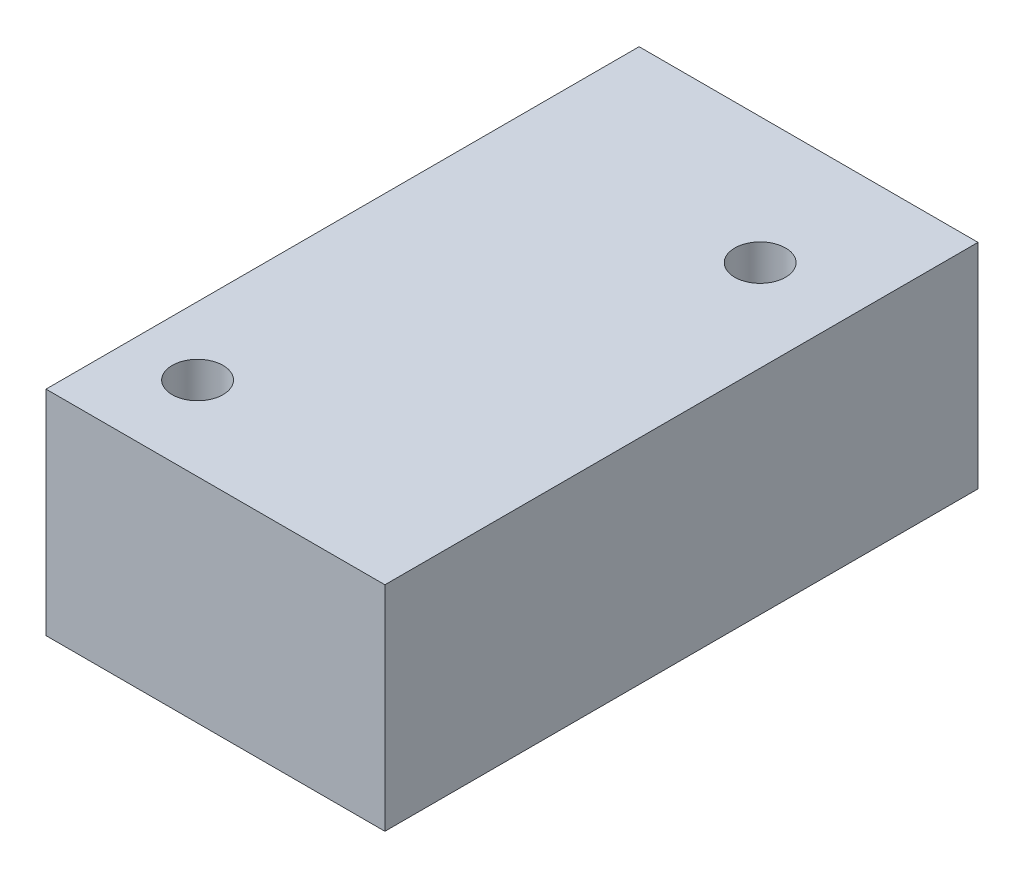
SolidWorks part; units mm, degrees
ref_plane "Front Plane" through (0, 0, 0) normal (0, 0, 1) x (1, 0, 0)
ref_plane "Top Plane" through (0, 0, 0) normal (0, 1, 0) x (1, 0, 0)
ref_plane "Right Plane" through (0, 0, 0) normal (1, 0, 0) x (0, 0, -1)
sketch "Sketch1" plane through (0, 0, 0) normal (0, 1, 0) x (1, 0, 0)
  line L1 (-10, 17.5) -> (10, 17.5)
  line L2 (-10, 17.5) -> (-10, -17.5)
  line L3 (-10, -17.5) -> (10, -17.5)
  line L4 (10, 17.5) -> (10, -17.5)
  line L5 (-10, 17.5) -> (10, -17.5) construction
  line L6 (-10, -17.5) -> (10, 17.5) construction
  point P0 (0, 0)
  dimension "D1" = 20
  dimension "D2" = 35
extrude "Boss-Extrude1" add sketch "Sketch1" along normal blind 12.6
sketch "Sketch2" plane through (0, 0, 0) normal (0, -1, 0) x (1, 0, 0)
  circle A0 centre (-5.9906, 12.5634) radius 1.5 construction
  circle A1 centre (4.6094, -10.0366) radius 1.5 construction
  circle A2 centre (-5.9906, 12.5634) radius 1.5
  circle A3 centre (4.6094, -10.0366) radius 1.5
extrude "Cut-Extrude1" cut sketch "Sketch2" against normal up to next
sketch "Sketch3" plane through (0, 0, 0) normal (0, 1, 0) x (1, 0, 0)
  line L4 (10, -17.5) -> (10, 17.5)
  line L5 (10, 17.5) -> (-10, 17.5)
  line L6 (-10, 17.5) -> (-10, -17.5)
  line L7 (-10, -17.5) -> (10, -17.5)
  line L8 (10, -17.5) -> (10, 17.5)
  line L9 (10, 17.5) -> (-10, 17.5)
  line L10 (-10, 17.5) -> (-10, -17.5)
  line L11 (-10, -17.5) -> (10, -17.5)
  circle A0 centre (4.6094, 10.0366) radius 1.5 construction
  circle A1 centre (-5.9906, -12.5634) radius 1.5 construction
  circle A2 centre (4.6094, 10.0366) radius 1.5
  circle A3 centre (-5.9906, -12.5634) radius 1.5
  dimension "D1" = 0
